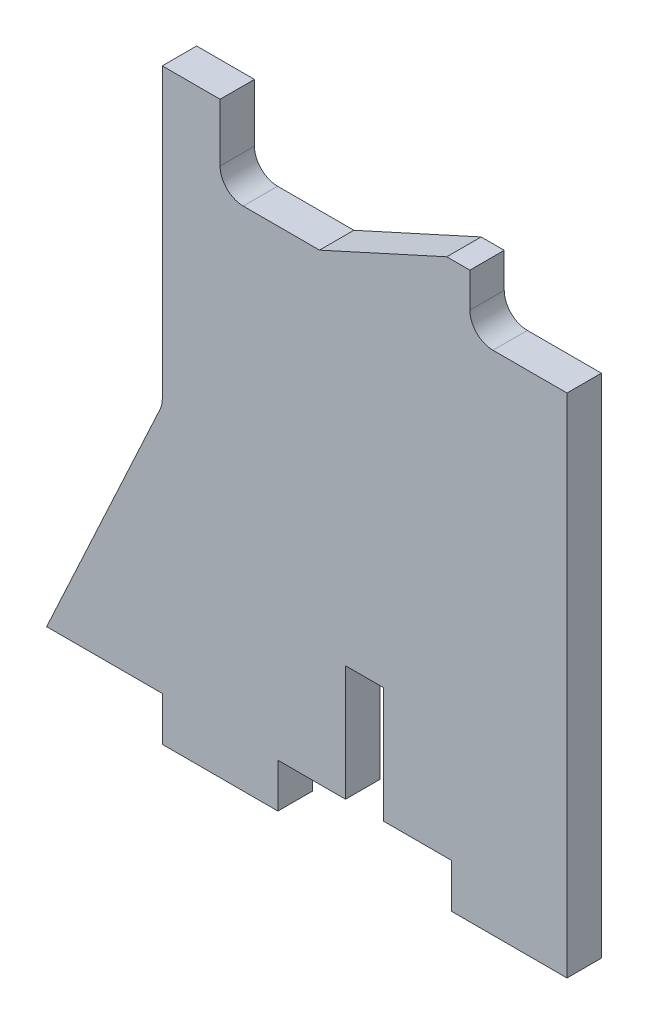
SolidWorks part; units mm, degrees
ref_plane "Front Plane" through (0, 0, 0) normal (0, 0, 1) x (1, 0, 0)
ref_plane "Top Plane" through (0, 0, 0) normal (0, 1, 0) x (1, 0, 0)
ref_plane "Right Plane" through (0, 0, 0) normal (1, 0, 0) x (0, 0, -1)
sketch "Sketch1" plane through (0, 0, 0) normal (0, 0, 1) x (1, 0, 0)
  line L1 (-17.5, -20) -> (17.5, -20)
  line L2 (-17.5, -20) -> (-17.5, 20)
  line L3 (-17.5, 20) -> (17.5, 20)
  line L4 (17.5, -20) -> (17.5, 20)
  line L5 (-17.5, -20) -> (17.5, 20) construction
  line L6 (-17.5, 20) -> (17.5, -20) construction
  point P0 (0, 0)
  dimension "D1" = 35
  dimension "D2" = 40
extrude "Boss-Extrude1" add sketch "Sketch1" along normal blind 2.9718
sketch "Sketch2" plane through (0, 0, 2.9718) normal (0, 0, 1) x (1, 0, 0)
  line L0 (-3.9004, 20) -> (7.0996, 25)
  line L1 (-17.5, 20) -> (-12.5, 20)
  line L2 (-17.5, 20) -> (-17.5, 27)
  line L3 (-17.5, 27) -> (-12.5, 27)
  line L4 (-12.5, 20) -> (-12.5, 27)
  line L5 (17.5, 20) -> (-17.5, 20) construction
  line L6 (7.0996, 25) -> (9.0996, 25)
  line L7 (9.0996, 25) -> (9.0996, 20)
  line L8 (-3.9004, 20) -> (9.0996, 20)
  line L10 (-17.5, -20) -> (-7.5, -20)
  line L11 (-17.5, -20) -> (-17.5, -23.81)
  line L12 (-17.5, -23.81) -> (-7.5, -23.81)
  line L13 (-7.5, -20) -> (-7.5, -23.81)
  line L14 (17.5, -20) -> (7.5, -20)
  line L15 (17.5, -20) -> (17.5, -23.81)
  line L16 (17.5, -23.81) -> (7.5, -23.81)
  line L17 (7.5, -20) -> (7.5, -23.81)
  dimension "D1" = 7
  dimension "D2" = 5
  dimension "D3" = 5
  dimension "D4" = 2
  dimension "D5" = 13
  dimension "D6" = 10
  dimension "D7" = 10
  dimension "D8" = 3.81
  dimension "D9" = 3.81
extrude "Boss-Extrude2" add sketch "Sketch2" against normal blind 2.9718
sketch "Sketch3" plane through (0, 0, 2.9718) normal (0, 0, 1) x (1, 0, 0)
  line L0 (-17.5, -20) -> (-27.5, -20)
  line L1 (-17.5, 27) -> (-17.5, -23.81) construction
  line L2 (-27.5, -20) -> (-17.5, 1.595)
  line L3 (-17.5, 1.595) -> (-17.5, -20)
  dimension "D1" = 10
extrude "Boss-Extrude3" add sketch "Sketch3" against normal blind 2.9718
fillet "Fillet1" radius 2 1 edges at (-12.5, 20, 1.4859)
fillet "Fillet2" radius 2 1 edges at (9.0996, 20, 1.4859)
fillet "Fillet3" radius 2 1 edges at (-17.5, 1.595, 1.4859)
sketch "Sketch4" plane through (0, 0, 2.9718) normal (0, 0, 1) x (1, 0, 0)
  line L0 (0, 0) -> (0, -20) construction
  line L1 (-7.5, -20) -> (7.5, -20) construction
  line L3 (-1.651, -20) -> (1.651, -20)
  line L4 (-1.651, -20) -> (-1.651, -10)
  line L5 (-1.651, -10) -> (1.651, -10)
  line L6 (1.651, -20) -> (1.651, -10)
  point P9 (0, -10)
  dimension "D1" = 10
  dimension "D2" = 3.302
extrude "Cut-Extrude1" cut sketch "Sketch4" against normal through all
